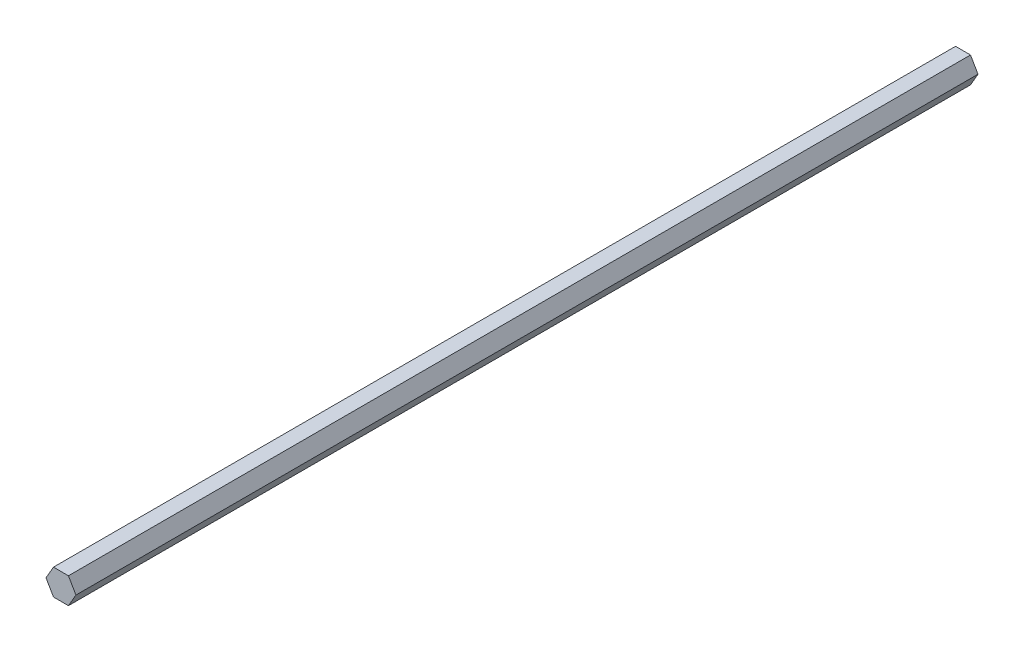
SolidWorks part; units mm, degrees
material "6061-T6 (SS)"
ref_plane "Front Plane" through (0, 0, 0) normal (0, 0, 1) x (1, 0, 0)
ref_plane "Top Plane" through (0, 0, 0) normal (0, 1, 0) x (1, 0, 0)
ref_plane "Right Plane" through (0, 0, 0) normal (1, 0, 0) x (0, 0, -1)
sketch "Sketch1" plane through (0, 0, 0) normal (0, 0, 1) x (1, 0, 0)
  line L1 (7.3323, 0) -> (3.6662, 6.35)
  line L2 (3.6662, 6.35) -> (-3.6662, 6.35)
  line L3 (-3.6662, 6.35) -> (-7.3323, 0)
  line L4 (-7.3323, 0) -> (-3.6662, -6.35)
  line L5 (-3.6662, -6.35) -> (3.6662, -6.35)
  line L6 (3.6662, -6.35) -> (7.3323, 0)
  circle A0 centre (0, 0) radius 6.35 construction
  dimension "D1" = 12.7
extrude "Boss-Extrude1" add sketch "Sketch1" along normal blind 441.96
